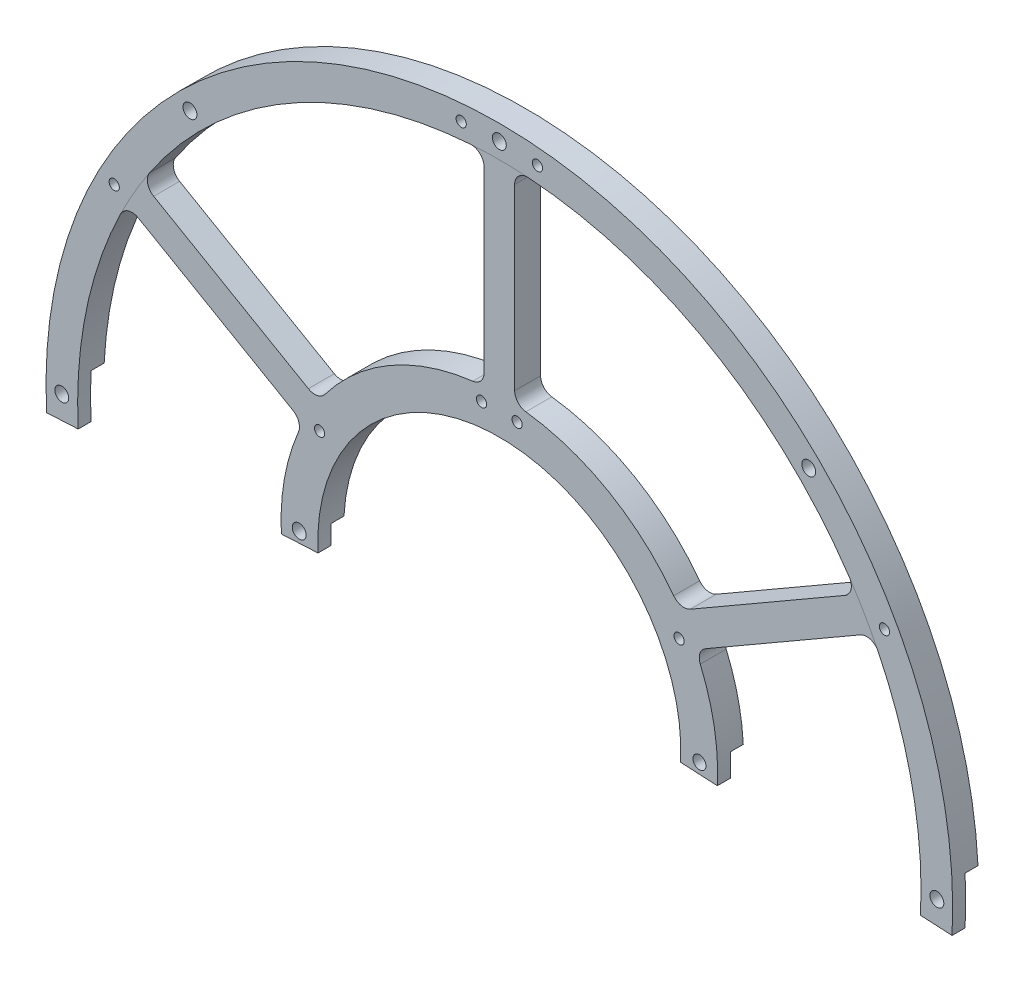
SolidWorks part; units mm, degrees
material "Dupont Vespel SP-1"
ref_plane "Front Plane" through (0, 0, 0) normal (0, 0, 1) x (1, 0, 0)
ref_plane "Top Plane" through (0, 0, 0) normal (0, 1, 0) x (1, 0, 0)
ref_plane "Right Plane" through (0, 0, 0) normal (1, 0, 0) x (0, 0, -1)
sketch "Sketch1" plane through (0, 0, 0) normal (0, 0, 1) x (1, 0, 0)
  circle A0 centre (0, 0) radius 111
  circle A1 centre (0, 0) radius 103.25
  circle A2 centre (0, 0) radius 44.45
  circle A3 centre (0, 0) radius 53.45
  dimension "D1" = 222
  dimension "D2" = 206.5
  dimension "D3" = 88.9
  dimension "D4" = 9
extrude "Boss-Extrude1" add sketch "Sketch1" along normal mid plane 6.35 contours A0 A1 | A3 A2
sketch "Sketch2" plane through (0, 0, 3.175) normal (0, 0, 1) x (1, 0, 0)
  line L0 (3.75, -53.3183) -> (3.75, -103.1819)
  line L1 (0, -103.25) -> (0, 0) construction
  line L2 (-3.75, -53.3183) -> (-3.75, -103.1819)
  circle A0 centre (0, 0) radius 53.45 construction
  circle A1 centre (0, 0) radius 103.25 construction
  circle A2 centre (0, 0) radius 53.45
  circle A3 centre (0, 0) radius 103.25
  circle M2 centre (0, 0) radius 103.25
  dimension "D1" = 7.5
extrude "Boss-Extrude2" add sketch "Sketch2" against normal through all contours L1 L0 A2 M2 | A3 L1 A2 L2
fillet "Fillet1" radius 3.125 4 edges at (3.75, -103.1819, 0) (-3.75, -103.1819, 0) (3.75, -53.3183, 0) (-3.75, -53.3183, 0)
pattern_circular "CirPattern2" count 6 over 360 about axis through (0, 0, 0) along (0, 0, 1) of "Boss-Extrude2", "Fillet1"
hole_wizard "M3 Clearance Hole1" positions "Sketch4" profile "Sketch3" hole size "M3" standard "Ansi Metric" end condition through all
sketch "Sketch4" plane through (0, 0, 3.175) normal (0, 0, 1) x (1, 0, 0)
  point P0 (0, 107.125)
  dimension "D1" = 107.125
sketch "Sketch3" plane through (0, 107.125, 3.175) normal (1, 0, 0) x (0, -1, 0)
  line L0 (0, 0) -> (0, 6.35)
  line L1 (0, 6.35) -> (1.7, 6.35)
  line L2 (1.7, 6.35) -> (1.7, 0)
  line L5 (1.7, 0) -> (0, 0)
  line L11 (0, -6.35) -> (0, 107.95) construction
  dimension "Thru Hole Dia." = 3.4
  dimension "Thru Hole Depth" = 6.35
pattern_circular "CirPattern3" count 8 over 360 about axis through (0, 0, 0) along (0, 0, 1) of "M3 Clearance Hole1"
sketch "Sketch5" plane through (0, 0, -3.175) normal (0, 0, -1) x (-1, 0, 0)
  line L0 (0, 0) -> (199.7259, -10.4672)
  line L1 (0, 0) -> (0, -111) construction
  line L2 (0, 0) -> (-199.7259, -10.4672)
  circle A0 centre (0, 0) radius 111 construction
  dimension "D1" = 87
  dimension "D2" = 200
extrude "Cut-Extrude1" cut sketch "Sketch5" against normal through all and the other way through all
sketch "Sketch6" plane through (0, 0, 0) normal (0, 0, 1) x (1, 0, 0)
  line L0 (0, 0) -> (199.7259, 10.4672)
  line L1 (0, 0) -> (0, 111) construction
  line L2 (0, 0) -> (111, 0) construction
  line L3 (0, 0) -> (199.7259, -10.4672) construction
  line L4 (199.7259, 10.4672) -> (199.7259, -44.2074)
  line L5 (103.1085, -5.4037) -> (110.8479, -5.8093) construction
  line L6 (199.7259, -44.2074) -> (0, 0)
  arc A0 (110.8479, -5.8093) -> (-110.8479, -5.8093) centre (0, 0) ccw construction
  dimension "D1" = 200
extrude "Cut-Extrude6" cut sketch "Sketch6" against normal blind 4
mirror "Mirror1" about plane through (0, 0, 0) normal (1, 0, 0) of "Cut-Extrude6"
sketch "Sketch7" plane through (0, 0, 3.175) normal (0, 0, 1) x (1, 0, 0)
  circle A0 centre (0, 0) radius 103.25
split line "Split Line1"
hole_wizard "M3 Clearance Hole2" positions "Sketch9" profile "Sketch10" hole size "M3" standard "Ansi Metric" end condition through all
sketch "Sketch9" plane through (0, 0, 3.175) normal (0, 0, 1) x (1, 0, 0)
  point P0 (-49, 0)
  dimension "D1" = 49
sketch "Sketch10" plane through (-49, 0, 3.175) normal (1, 0, 0) x (0, -1, 0)
  line L0 (0, 0) -> (0, 6.35)
  line L1 (0, 6.35) -> (1.7, 6.35)
  line L2 (1.7, 6.35) -> (1.7, 0)
  line L5 (1.7, 0) -> (0, 0)
  line L11 (0, -6.35) -> (0, 107.95) construction
  dimension "Thru Hole Dia." = 3.4
  dimension "Thru Hole Depth" = 6.35
hole_wizard "M3 Clearance Hole3" positions "Sketch12" profile "Sketch11" hole size "M3" standard "Ansi Metric" end condition through all
sketch "Sketch12" plane through (0, 0, 3.175) normal (0, 0, 1) x (1, 0, 0)
  point P0 (49, 0)
  dimension "D1" = 49
sketch "Sketch11" plane through (49, 0, 3.175) normal (1, 0, 0) x (0, -1, 0)
  line L0 (0, 0) -> (0, 6.35)
  line L1 (0, 6.35) -> (1.6, 6.35)
  line L2 (1.6, 6.35) -> (1.6, 0)
  line L5 (1.6, 0) -> (0, 0)
  line L11 (0, -6.35) -> (0, 107.95) construction
  dimension "Thru Hole Dia." = 3.2
  dimension "Thru Hole Depth" = 6.35
hole_wizard "M3x0.5 Tapped Hole1" positions "Sketch14" profile "Sketch13" tap size "M3x0.5" standard "Ansi Metric" end condition through all
sketch "Sketch14" plane through (0, 0, -3.175) normal (0, 0, -1) x (-1, 0, 0)
  point P0 (-9.3366, 106.7174)
  point P4 (-94.2916, 50.8416)
  point P7 (-44.0101, 23.73)
  point P10 (-4.3578, 49.8097)
  point P13 (4.3578, 49.8097)
  point P16 (44.0101, 23.73)
  point P19 (94.2916, 50.8416)
  point P22 (9.3366, 106.7174)
sketch "Sketch13" plane through (9.3366, 106.7174, -3.175) normal (1, 0, 0) x (0, 1, 0)
  line L0 (0, 0) -> (0, 6.35)
  line L1 (0, 6.35) -> (1.25, 6.35)
  line L2 (1.25, 6.35) -> (1.25, 0)
  line L5 (1.25, 0) -> (0, 0)
  line L11 (0, -6.35) -> (0, 107.95) construction
  dimension "Thru Tap Drill Dia." = 2.5
  dimension "Thru Tap Drill Depth" = 6.35
cosmetic thread "Hole Thread5" parameters "D2"=3
cosmetic thread "Hole Thread6" parameters "D2"=3
cosmetic thread "Hole Thread7" parameters "D2"=3
cosmetic thread "Hole Thread8" parameters "D2"=3
cosmetic thread "Hole Thread9" parameters "D2"=3
cosmetic thread "Hole Thread10" parameters "D2"=3
cosmetic thread "Hole Thread11" parameters "D2"=3
cosmetic thread "Hole Thread12" parameters "D2"=3
